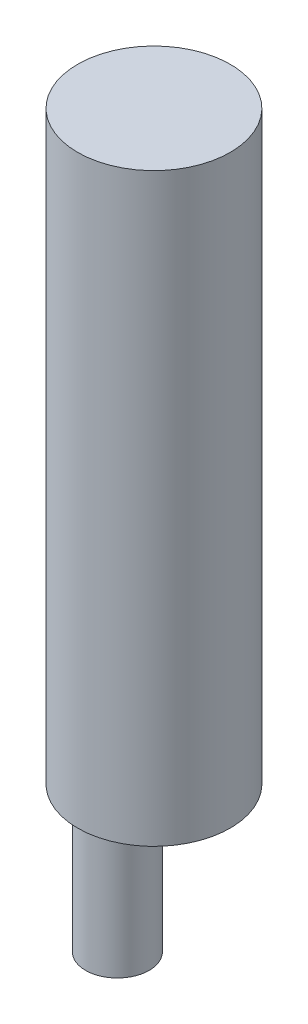
SolidWorks part; units mm, degrees
ref_plane "Front Plane" through (0, 0, 0) normal (0, 0, 1) x (1, 0, 0)
ref_plane "Top Plane" through (0, 0, 0) normal (0, 1, 0) x (1, 0, 0)
ref_plane "Right Plane" through (0, 0, 0) normal (1, 0, 0) x (0, 0, -1)
sketch "Sketch1" plane through (0, 0, 0) normal (0, 1, 0) x (1, 0, 0)
  circle A0 centre (0, 0) radius 9
extrude "Boss-Extrude1" add sketch "Sketch1" along normal mid plane 69
sketch "Sketch2" plane through (0, -34.5, 0) normal (0, -1, 0) x (1, 0, 0)
  line L0 (0, -9.9) -> (0, 9.9) construction
  circle A0 centre (0, 4.3106) radius 3.75
extrude "Boss-Extrude2" add sketch "Sketch2" along normal blind 15
